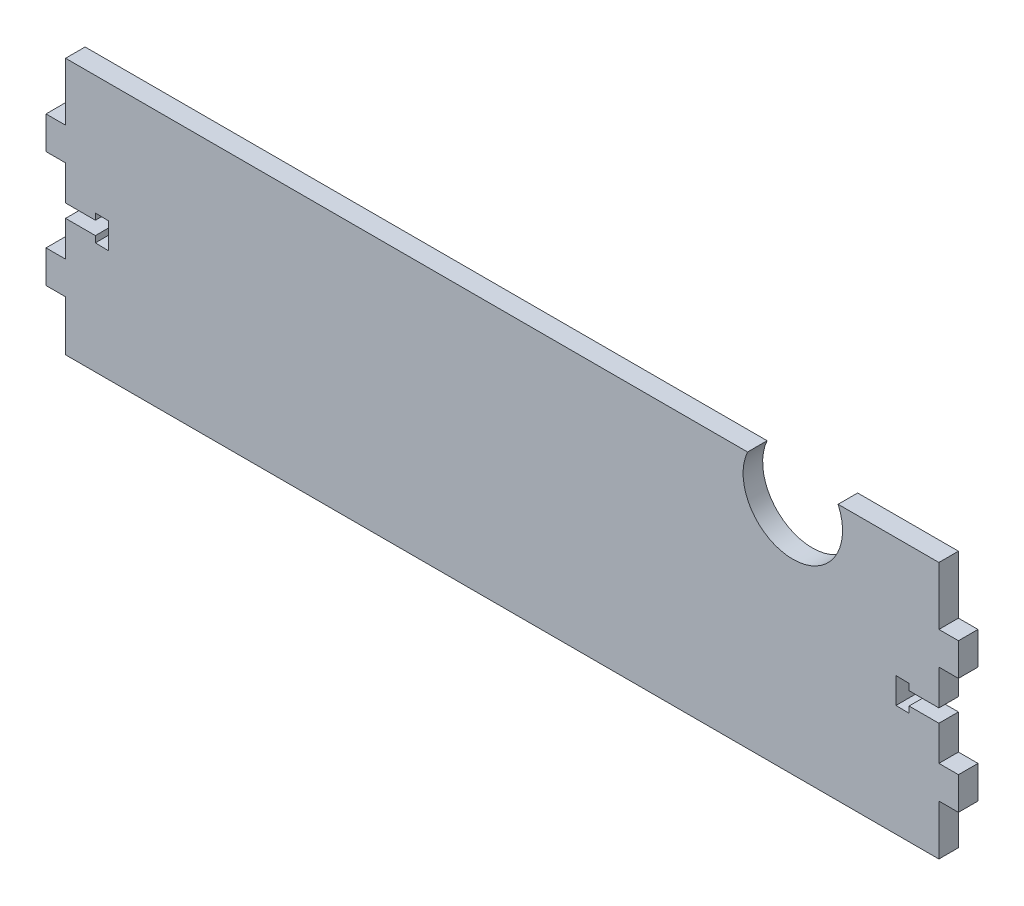
SolidWorks part; units mm, degrees
ref_plane "Front Plane" through (0, 0, 0) normal (0, 0, 1) x (1, 0, 0)
ref_plane "Top Plane" through (0, 0, 0) normal (0, 1, 0) x (1, 0, 0)
ref_plane "Right Plane" through (0, 0, 0) normal (1, 0, 0) x (0, 0, -1)
sketch "Sketch1" plane through (0, 0, 0) normal (0, 0, 1) x (1, 0, 0)
  line L0 (-195.9156, 39.8641) -> (-204.4805, 39.8641) construction
  line L1 (-209.0596, -29.4779) -> (58.6564, -29.4779)
  line L2 (-209.0596, -29.4779) -> (-209.0596, 49.2621)
  line L3 (-209.0596, 49.2621) -> (58.6564, 49.2621)
  line L4 (58.6564, -29.4779) -> (58.6564, 49.2621)
  line L5 (-195.9156, 8.7021) -> (-202.3632, 8.7021) construction
  line L6 (-75.2016, 49.2621) -> (-75.2016, -29.4779) construction
  line L7 (45.5124, 39.8641) -> (55.3041, 39.8641) construction
  line L9 (45.5124, 8.7021) -> (52.0122, 8.7021) construction
  arc A0 (27.7563, 49.2621) -> (0, 49.2621) centre (13.8782, 42.965) cw
  line B0 (-215.054, 26.4821) -> (-209.0596, 26.4821) construction
  line B1 (-215.054, 21.4821) -> (-215.054, 31.4821)
  line B2 (-215.054, 21.4821) -> (-209.0596, 21.4821)
  line B3 (-209.0596, 21.4821) -> (-209.0596, 31.4821)
  line B4 (-215.054, 31.4821) -> (-209.0596, 31.4821)
  line B5 (-215.054, -9.0779) -> (-209.0596, -9.0779) construction
  line B6 (-215.054, -14.0779) -> (-215.054, -4.0779)
  line B7 (-215.054, -14.0779) -> (-209.0596, -14.0779)
  line B8 (-209.0596, -14.0779) -> (-209.0596, -4.0779)
  line B9 (-215.054, -4.0779) -> (-209.0596, -4.0779)
  line B10 (58.6564, 26.4821) -> (64.6508, 26.4821) construction
  line B11 (58.6564, 21.4821) -> (58.6564, 31.4821)
  line B12 (58.6564, 21.4821) -> (64.6508, 21.4821)
  line B13 (64.6508, 21.4821) -> (64.6508, 31.4821)
  line B14 (58.6564, 31.4821) -> (64.6508, 31.4821)
  line B15 (58.6564, -9.0779) -> (64.6508, -9.0779) construction
  line B16 (58.6564, -14.0779) -> (58.6564, -4.0779)
  line B17 (58.6564, -14.0779) -> (64.6508, -14.0779)
  line B18 (64.6508, -14.0779) -> (64.6508, -4.0779)
  line B19 (58.6564, -4.0779) -> (64.6508, -4.0779)
  line B20 (-209.0596, 6.7587) -> (-199.9156, 6.7587)
  line B21 (-199.9156, 6.7587) -> (-199.9156, 4.822)
  line B22 (-199.9156, 4.822) -> (-195.9156, 4.7334)
  line B23 (-195.9156, 4.7334) -> (-195.9156, 12.6709)
  line B24 (-195.9156, 12.6709) -> (-199.9156, 12.7595)
  line B25 (-199.9156, 12.7595) -> (-199.9156, 10.8227)
  line B26 (-199.9156, 10.8227) -> (-209.0596, 10.8227)
  line B27 (-209.0596, 37.9207) -> (-199.9156, 37.9207)
  line B28 (-199.9156, 37.9207) -> (-199.9156, 35.984)
  line B29 (-199.9156, 35.984) -> (-195.9156, 35.8954)
  line B30 (-195.9156, 35.8954) -> (-195.9156, 43.8329)
  line B31 (-195.9156, 43.8329) -> (-199.9156, 43.9215)
  line B32 (-199.9156, 43.9215) -> (-199.9156, 41.9847)
  line B33 (-199.9156, 41.9847) -> (-209.0596, 41.9847)
  line B34 (58.6564, 41.8075) -> (49.5124, 41.8075)
  line B35 (49.5124, 41.8075) -> (49.5124, 43.7443)
  line B36 (49.5124, 43.7443) -> (45.5124, 43.8329)
  line B37 (45.5124, 43.8329) -> (45.5124, 35.8954)
  line B38 (45.5124, 35.8954) -> (49.5124, 35.8068)
  line B39 (49.5124, 35.8068) -> (49.5124, 37.7435)
  line B40 (49.5124, 37.7435) -> (58.6564, 37.7435)
  line B41 (58.6564, 10.6455) -> (49.5124, 10.6455)
  line B42 (49.5124, 10.6455) -> (49.5124, 12.5823)
  line B43 (49.5124, 12.5823) -> (45.5124, 12.6709)
  line B44 (45.5124, 12.6709) -> (45.5124, 4.7334)
  line B45 (45.5124, 4.7334) -> (49.5124, 4.6448)
  line B46 (49.5124, 4.6448) -> (49.5124, 6.5815)
  line B47 (49.5124, 6.5815) -> (58.6564, 6.5815)
sketch_block_instance "Block1-6"
sketch_block "Block1" parameters "D1"=4.2151, "D2"=10.103, "D3"=7.4845
sketch_block_instance "Block1-8"
sketch_block_instance "Block1-10"
sketch_block_instance "extrusionblock-1"
sketch_block "extrusionblock" parameters "D1"=5.9944, "D2"=10
sketch_block_instance "extrusionblock-2"
sketch_block_instance "extrusionblock-4"
sketch_block_instance "extrusionblock-5"
sketch_block_instance "screwblock-1"
sketch_block "screwblock" parameters "D1"=4.2151, "D2"=10.103, "D3"=7.4845, "D4"=1.829
sketch_block_instance "screwblock-2"
sketch_block_instance "screwblock-4"
sketch_block_instance "screwblock-8" parameters "D11"=19.4391, "D1"=50.2589, "D2"=106.8002, "D3"=7.8019, "D4"=18.775, "D5"=20.1789, "D6"=17.78, "D7"=18.1825, "D8"=17.3775, "D9"=6.5837, "D10"=9.4209
extrude "Extrude1" add sketch "Sketch1" along normal blind 5.9944 contours B47 B46 B45 B44 B43 B42 B41 L4 B40 B39 B38 B37 B36 B35 B34 L3 L2 B33 B32 B31 B30 B29 B28 B27 B26 B25 B24 B23 B22 B21 B20 L1 | B14 L4 B12 B13 | B19 L4 B17 B18 | B4 B1 B2 L2 | B9 B6 B7 L2 | B32 B33 L2 B27 B28 B29 B30 B31 | B39 B40 L4 B34 B35 B36 B37 B38
